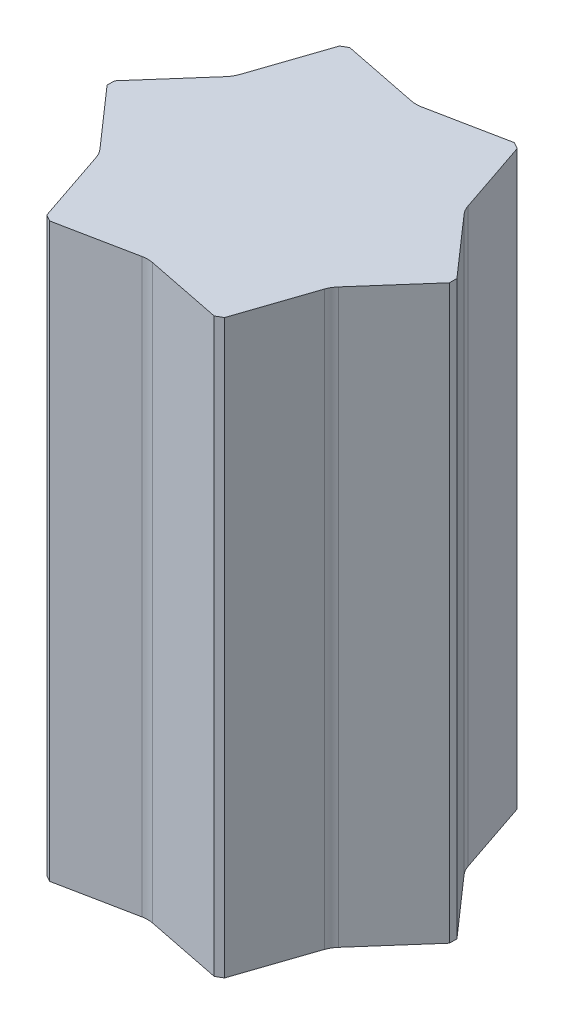
SolidWorks part; units mm, degrees
material "PEN"
ref_plane "前视基准面" through (0, 0, 0) normal (0, 0, 1) x (1, 0, 0)
ref_plane "上视基准面" through (0, 0, 0) normal (0, 1, 0) x (1, 0, 0)
ref_plane "右视基准面" through (0, 0, 0) normal (1, 0, 0) x (0, 0, -1)
sketch "草图1" plane through (0, 0, 0) normal (0, 1, 0) x (1, 0, 0)
  line L1 (395, 8.6603) -> (205, 337.7499)
  line L2 (190, 346.4102) -> (-190, 346.4102)
  line L3 (-205, 337.7499) -> (-395, 8.6603)
  line L4 (-395, -8.6603) -> (-205, -337.7499)
  line L5 (-190, -346.4102) -> (190, -346.4102)
  line L6 (205, -337.7499) -> (395, -8.6603)
  line L8 (190, 346.4102) -> (205, 337.7499)
  line L10 (395, -8.6603) -> (395, 8.6603)
  line L12 (205, -337.7499) -> (190, -346.4102)
  line L14 (-395, 8.6603) -> (-395, -8.6603)
  line L18 (-190, 346.4102) -> (-205, 337.7499)
  line L20 (-190, -346.4102) -> (-205, -337.7499)
extrude "凸台-拉伸1" add sketch "草图1" along normal mid plane 1320
sketch "草图4" plane through (0, 0, 0) normal (0, 1, 0) x (1, 0, 0)
  line L1 (190, 369.6203) -> (190, 346.4102)
  line L2 (11.76, 310.7841) -> (190, 346.4102)
  line L3 (-190, 346.4102) -> (-11.76, 310.7841)
  line L4 (-190, 369.6203) -> (-190, 346.4102)
  line L6 (-190, 369.6203) -> (-190, 392.8305)
  line L8 (-11.76, 428.4566) -> (-190, 392.8305)
  line L9 (190, 392.8305) -> (11.76, 428.4566)
  line L10 (190, 369.6203) -> (190, 392.8305)
  line L11 (415.1006, 20.2653) -> (395, 8.6603)
  line L17 (275.0269, 145.2076) -> (395, 8.6603)
  line L18 (205, 337.7499) -> (263.2669, 165.5765)
  line L19 (225.1006, 349.355) -> (205, 337.7499)
  line L20 (225.1006, 349.355) -> (245.2012, 360.9601)
  line L21 (365.1743, 224.4127) -> (245.2012, 360.9601)
  line L22 (435.2012, 31.8704) -> (376.9343, 204.0438)
  line L23 (415.1006, 20.2653) -> (435.2012, 31.8704)
  line L24 (225.1006, -349.355) -> (205, -337.7499)
  line L25 (263.2669, -165.5765) -> (205, -337.7499)
  line L26 (395, -8.6603) -> (275.0269, -145.2076)
  line L27 (415.1006, -20.2653) -> (395, -8.6603)
  line L28 (415.1006, -20.2653) -> (435.2012, -31.8704)
  line L29 (376.9343, -204.0438) -> (435.2012, -31.8704)
  line L30 (245.2012, -360.9601) -> (365.1743, -224.4127)
  line L31 (225.1006, -349.355) -> (245.2012, -360.9601)
  line L32 (-190, -369.6203) -> (-190, -346.4102)
  line L33 (-11.76, -310.7841) -> (-190, -346.4102)
  line L34 (190, -346.4102) -> (11.76, -310.7841)
  line L35 (190, -369.6203) -> (190, -346.4102)
  line L36 (190, -369.6203) -> (190, -392.8305)
  line L37 (11.76, -428.4566) -> (190, -392.8305)
  line L38 (-190, -392.8305) -> (-11.76, -428.4566)
  line L39 (-190, -369.6203) -> (-190, -392.8305)
  line L40 (-415.1006, -20.2653) -> (-395, -8.6603)
  line L41 (-275.0269, -145.2076) -> (-395, -8.6603)
  line L42 (-205, -337.7499) -> (-263.2669, -165.5765)
  line L43 (-225.1006, -349.355) -> (-205, -337.7499)
  line L44 (-225.1006, -349.355) -> (-245.2012, -360.9601)
  line L45 (-365.1743, -224.4127) -> (-245.2012, -360.9601)
  line L46 (-435.2012, -31.8704) -> (-376.9343, -204.0438)
  line L47 (-415.1006, -20.2653) -> (-435.2012, -31.8704)
  line L48 (-225.1006, 349.355) -> (-205, 337.7499)
  line L49 (-263.2669, 165.5765) -> (-205, 337.7499)
  line L50 (-395, 8.6603) -> (-275.0269, 145.2076)
  line L51 (-415.1006, 20.2653) -> (-395, 8.6603)
  line L52 (-415.1006, 20.2653) -> (-435.2012, 31.8704)
  line L53 (-376.9343, 204.0438) -> (-435.2012, 31.8704)
  line L54 (-245.2012, 360.9601) -> (-365.1743, 224.4127)
  line L55 (-225.1006, 349.355) -> (-245.2012, 360.9601)
  arc A0 (-11.76, 310.7841) -> (11.76, 310.7841) centre (0, 369.6203) ccw
  arc A1 (11.76, 428.4566) -> (-11.76, 428.4566) centre (0, 369.6203) ccw
  arc A2 (263.2669, 165.5765) -> (275.0269, 145.2076) centre (320.1006, 184.8102) ccw
  arc A3 (376.9343, 204.0438) -> (365.1743, 224.4127) centre (320.1006, 184.8102) ccw
  arc A4 (275.0269, -145.2076) -> (263.2669, -165.5765) centre (320.1006, -184.8102) ccw
  arc A5 (365.1743, -224.4127) -> (376.9343, -204.0438) centre (320.1006, -184.8102) ccw
  arc A8 (11.76, -310.7841) -> (-11.76, -310.7841) centre (0, -369.6203) ccw
  arc A9 (-11.76, -428.4566) -> (11.76, -428.4566) centre (0, -369.6203) ccw
  arc A10 (-263.2669, -165.5765) -> (-275.0269, -145.2076) centre (-320.1006, -184.8102) ccw
  arc A11 (-376.9343, -204.0438) -> (-365.1743, -224.4127) centre (-320.1006, -184.8102) ccw
  arc A12 (-275.0269, 145.2076) -> (-263.2669, 165.5765) centre (-320.1006, 184.8102) ccw
  arc A13 (-365.1743, 224.4127) -> (-376.9343, 204.0438) centre (-320.1006, 184.8102) ccw
  dimension "D1" = 6
extrude "切除-拉伸1" cut sketch "草图4" against normal through all both and the other way through all
shell "抽壳1" thickness 10
sketch "草图5" plane through (0, 0, 0) normal (0, 0, 1) x (1, 0, 0)
  line L0 (0, -660) -> (0, 660)
  line L1 (-11.76, -660) -> (11.76, -660) construction
  line L2 (11.76, 660) -> (-11.76, 660) construction
